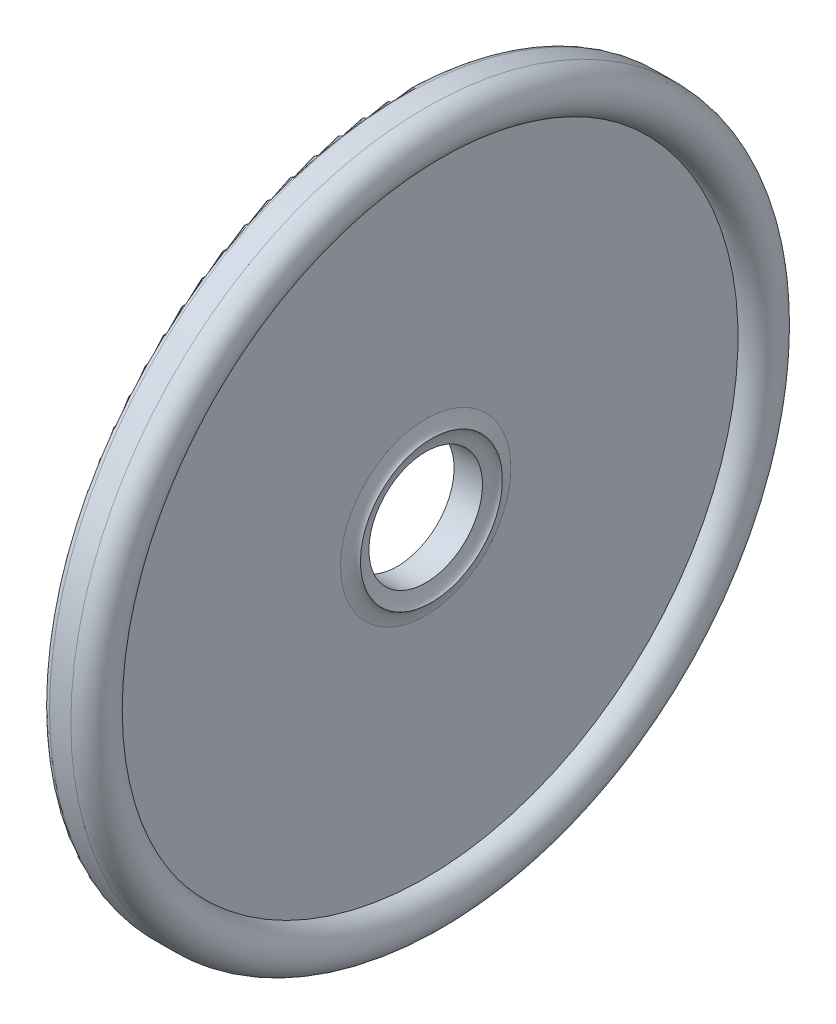
SolidWorks part; units mm, degrees
material "ABS"
ref_plane "Front Plane" through (0, 0, 0) normal (0, 0, 1) x (1, 0, 0)
ref_plane "Top Plane" through (0, 0, 0) normal (0, 1, 0) x (1, 0, 0)
ref_plane "Right Plane" through (0, 0, 0) normal (1, 0, 0) x (0, 0, -1)
sketch "Sketch1" plane through (0, 0, 0) normal (0, 0, -1) x (-1, 0, 0)
  line L9 (0, 2.5) -> (-1.2, 2.5) construction
  line L10 (1.4433, 0) -> (-2.0619, 0) construction
  line L11 (-1, 11) -> (-1, 3)
  line L12 (0, 2) -> (-1, 2)
  line L13 (0, 12.25) -> (0, 2)
  line L14 (-0.25, 12.5) -> (-1, 12.5)
  arc A4 (-0.25, 12.5) -> (0, 12.25) centre (-0.25, 12.25) cw
  arc A5 (-1, 12.5) -> (-1, 11) centre (-1, 11.75) ccw
  spline S2 degree 2 poles (-1, 2) (-1.0782, 2.4243) (-1.2, 2.5) knots 0 0 0 0.432994 0.432994 0.432994
  spline S3 degree 2 poles (-1, 3) (-1.0782, 2.5757) (-1.2, 2.5) knots 0 0 0 0.432994 0.432994 0.432994
  dimension "D7" = 0.75
  dimension "D3" = 0.75
  dimension "D8" = 1
  dimension "D2" = 1.2
  dimension "D4" = 0.25
  dimension "D1" = 4
  dimension "D5" = 10.25
  dimension "D6" = 8
revolve "Revolve1" add sketch "Sketch1" angle 360 about L10
